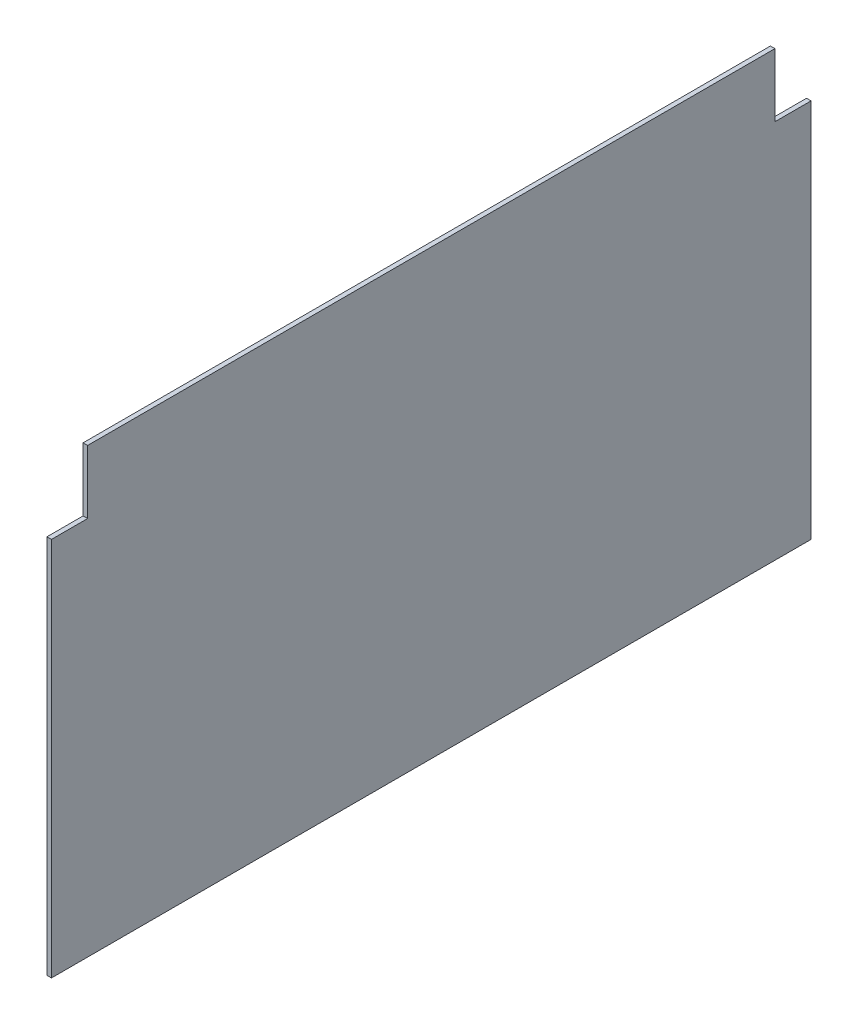
SolidWorks part; units mm, degrees
material "PC High Viscosity"
ref_plane "Front Plane" through (0, 0, 0) normal (0, 0, 1) x (1, 0, 0)
ref_plane "Top Plane" through (0, 0, 0) normal (0, 1, 0) x (1, 0, 0)
ref_plane "Right Plane" through (0, 0, 0) normal (1, 0, 0) x (0, 0, -1)
sketch "Sketch1" plane through (0, 0, 0) normal (1, 0, 0) x (0, 0, -1)
  line L0 (1016, 533.4) -> (1066.8, 533.4)
  line L1 (0, 0) -> (1066.8, 0)
  line L2 (0, 0) -> (0, 533.4)
  line L3 (0, 533.4) -> (50.8, 533.4)
  line L4 (1066.8, 0) -> (1066.8, 533.4)
  line L6 (50.8, 533.4) -> (50.8, 622.3)
  line L8 (1016, 533.4) -> (1016, 622.3)
  line L13 (50.8, 622.3) -> (1016, 622.3)
  dimension "D1" = 1066.8
  dimension "D2" = 533.4
  dimension "D3" = 50.8
  dimension "D4" = 50.8
  dimension "D5" = 88.9
  dimension "D6" = 965.2
extrude "Boss-Extrude1" add sketch "Sketch1" along normal blind 6.35
sketch "Sketch2" plane through (6.35, 0, 0) normal (1, 0, 0) x (0, 0, -1)
  line L1 (0, 0) -> (1066.8, 0) construction
  line L2 (149.225, 95.25) -> (171.0336, 121.2405)
  line L3 (171.0336, 121.2405) -> (157.0619, 164.2411)
  line L4 (157.0619, 164.2411) -> (247.65, 193.675)
  line L5 (247.65, 193.675) -> (276.0453, 106.2834)
  line L7 (0, 533.4) -> (0, 0) construction
  line L9 (863.6, 297.1915) -> (863.6, 622.3)
  line L10 (1016, 622.3) -> (50.8, 622.3) construction
  line L11 (863.6, 622.3) -> (1016, 622.3)
  line L12 (1016, 622.3) -> (1016, 533.4)
  line L13 (1016, 533.4) -> (1066.8, 533.4)
  line L14 (1066.8, 533.4) -> (1066.8, 0)
  line L15 (1066.8, 0) -> (0, 0)
  line L16 (50.8, 622.3) -> (50.8, 533.4) construction
  line L17 (0, 114.3) -> (44.45, 114.3)
  line L18 (0, 114.3) -> (0, 0)
  line L20 (44.45, 114.3) -> (44.45, 31.0335)
  line L21 (59.3115, 45.8775) -> (771.9221, 277.4187) construction
  line L22 (276.0453, 106.2834) -> (863.6, 297.1915)
  line L23 (149.225, 95.25) -> (149.225, 65.077)
  line L24 (149.225, 65.077) -> (44.45, 31.0335)
  line L26 (134.9375, 487.7489) -> (219.4864, 515.2205) construction
  line L27 (0, 317.5) -> (44.45, 317.5)
  line L28 (0, 317.5) -> (0, 273.05)
  line L29 (0, 273.05) -> (44.45, 273.05)
  line L30 (44.45, 317.5) -> (44.45, 273.05)
  circle A0 centre (59.3115, 45.8775) radius 2.4575
  circle A1 centre (296.8457, 123.057) radius 2.4574
  circle A2 centre (534.3799, 200.2365) radius 2.4575
  circle A3 centre (771.9221, 277.4187) radius 2.4575
  circle A4 centre (854.075, 309.0545) radius 2.4575
  circle A5 centre (854.075, 486.8545) radius 2.4575
  circle A6 centre (219.4864, 515.2205) radius 2.4574
  circle A7 centre (134.9375, 487.7489) radius 2.4575
  circle A8 centre (88.9, 584.2) radius 22.225
  dimension "D19" = 134.9375
  dimension "D23" = 4.9149
  dimension "D32" = 44.45
  dimension "D33" = 203.2
  dimension "D10" = 249.7582
  dimension "D11" = 249.7667
  dimension "D14" = 9.525
  dimension "D2" = 95.25
  dimension "D4" = 18
  dimension "D5" = 193.675
  dimension "D6" = 247.65
  dimension "D7" = 249.7582
  dimension "D8" = 45.8775
  dimension "D9" = 59.3115
  dimension "D12" = 122
  dimension "D13" = 9.525
  dimension "D15" = 9.525
  dimension "D16" = 854.075
  dimension "D17" = 486.8545
  dimension "D18" = 309.0545
  dimension "D20" = 396.875
  dimension "D21" = 88.9
  dimension "D24" = 149.225
  dimension "D25" = 95.25
  dimension "D26" = 44.45
  dimension "D27" = 114.3
  dimension "D28" = 44.45
  dimension "D29" = 44.45
  dimension "D30" = 38.1
  dimension "D31" = 38.1
extrude "Cut-Extrude1" [suppressed] cut sketch "Sketch2" against normal through all
fillet "Fillet1" [suppressed] radius 3.175
